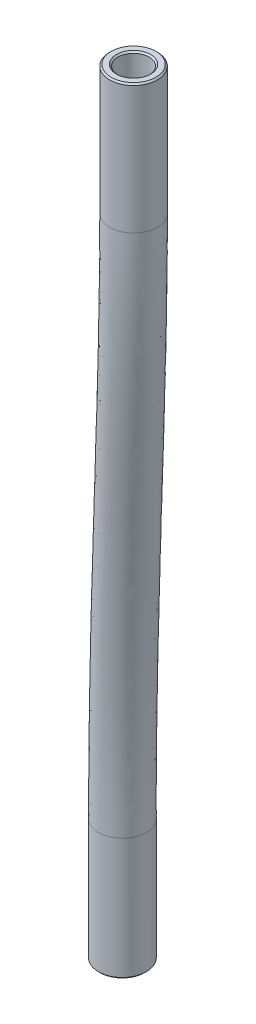
SolidWorks part; units mm, degrees
ref_plane "Front Plane" through (0, 0, 0) normal (0, 0, 1) x (1, 0, 0)
ref_plane "Top Plane" through (0, 0, 0) normal (0, 1, 0) x (1, 0, 0)
ref_plane "Right Plane" through (0, 0, 0) normal (1, 0, 0) x (0, 0, -1)
sketch3d "3DSketch1"
  line L0 (-150.0853, -93.2823, -9.525) -> (-150.0853, -103.4823, -9.525)
  line L1 (-146.7276, -35.8, -7.0985) -> (-146.7276, -46.6, -7.0985)
  spline S0 degree 3 poles (-146.7276, -46.6, -7.0985) (-146.7276, -53.2688, -7.0985) (-148.4064, -68.8049, -8.3118) (-150.0853, -84.313, -9.525) (-150.0853, -93.2823, -9.525) knots 0 0 0 0 0.426886 1 1 1 1
sketch "Sketch1" plane through (0, -95.3823, 0) normal (0, 1, 0) x (1, 0, 0)
  circle A0 centre (-150.0853, 9.525) radius 2
  circle A1 centre (-150.0853, 9.525) radius 3.6 construction
  circle A2 centre (-150.0853, 9.525) radius 1.3
  dimension "D1" = 4
  dimension "D2" = 2.6
sweep "Sweep1" add profiles "Sketch1" path "3DSketch1"
chamfer "Chamfer1" distance 0.127 angle 45 4 edges at (-152.0853, -103.4823, -9.525) (-151.3853, -103.4823, -9.525) (-148.7276, -35.8, -7.0985) (-148.0276, -35.8, -7.0985)
